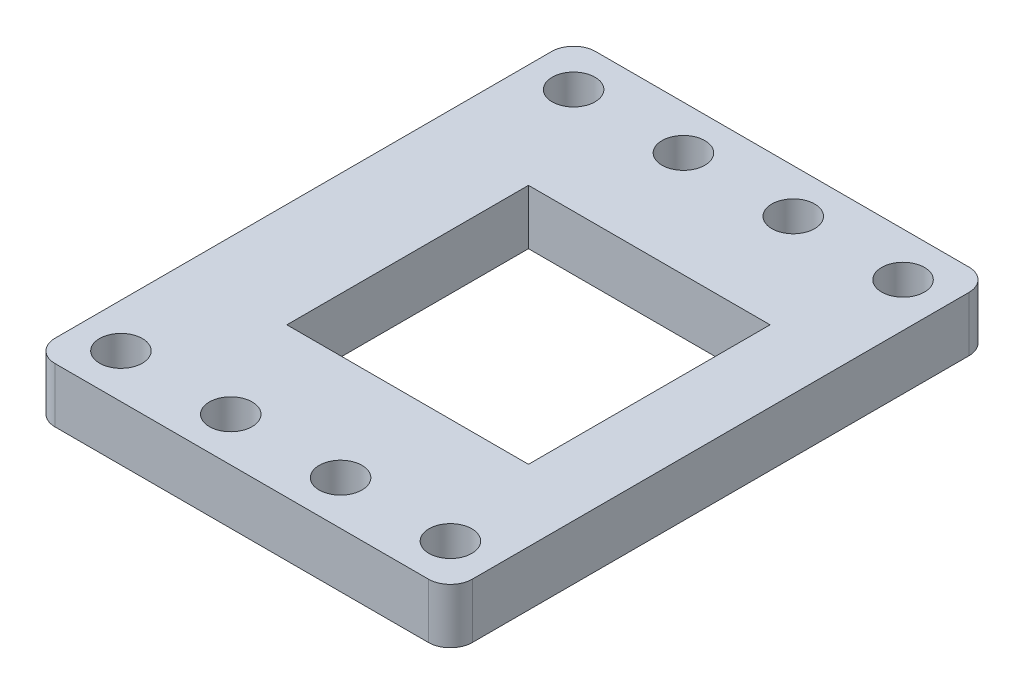
SolidWorks part; units mm, degrees
ref_plane "Front Plane" through (0, 0, 0) normal (0, 0, 1) x (1, 0, 0)
ref_plane "Top Plane" through (0, 0, 0) normal (0, 1, 0) x (1, 0, 0)
ref_plane "Right Plane" through (0, 0, 0) normal (1, 0, 0) x (0, 0, -1)
sketch "Sketch1" plane through (0, 0, 0) normal (0, 1, 0) x (1, 0, 0)
  line L1 (-36, 0) -> (-2, 0)
  line L2 (-38, -2) -> (-38, -47.22)
  line L3 (-36, -49.22) -> (-2, -49.22)
  line L4 (0, -2) -> (0, -47.22)
  arc A0 (-2, -49.22) -> (0, -47.22) centre (-2, -47.22) ccw
  arc A1 (-38, -47.22) -> (-36, -49.22) centre (-36, -47.22) ccw
  arc A2 (-36, 0) -> (-38, -2) centre (-36, -2) ccw
  arc A3 (-2, 0) -> (0, -2) centre (-2, -2) cw
  point P7 (0, -49.22)
  point P12 (-38, 0)
  point P15 (0, 0)
  dimension "D3" = 2
  dimension "D1" = 38
  dimension "D2" = 49.22
extrude "Boss-Extrude1" add sketch "Sketch1" along normal blind 5
sketch "Sketch2" plane through (0, 5, 0) normal (0, 1, 0) x (1, 0, 0)
  line L0 (-2, 0) -> (-36, 0) construction
  line L1 (0, -47.22) -> (0, -2) construction
  line L2 (-4, -4) -> (-54, -4) construction
  line L4 (-4, -45.22) -> (-54, -45.22) construction
  line L5 (-36, -49.22) -> (-2, -49.22) construction
  line L6 (-28.5, -24.61) -> (-6.5, -24.61) construction
  line L7 (-28.5, -13.61) -> (-6.5, -13.61)
  line L8 (-28.5, -13.61) -> (-28.5, -35.61)
  line L9 (-28.5, -35.61) -> (-6.5, -35.61)
  line L10 (-6.5, -13.61) -> (-6.5, -35.61)
  circle A20 centre (-4, -4) radius 1.95
  circle A21 centre (-14, -4) radius 1.95
  circle A22 centre (-24, -4) radius 1.95
  circle A23 centre (-54, -4) radius 1.95
  circle A24 centre (-34, -4) radius 1.95
  circle A25 centre (-44, -4) radius 1.95
  circle A26 centre (-44, -45.22) radius 1.95
  circle A27 centre (-34, -45.22) radius 1.95
  circle A28 centre (-54, -45.22) radius 1.95
  circle A29 centre (-24, -45.22) radius 1.95
  circle A30 centre (-14, -45.22) radius 1.95
  circle A31 centre (-4, -45.22) radius 1.95
  dimension "D1" = 10
  dimension "D7" = 3.9
  dimension "D8" = 3.9
  dimension "D9" = 3.9
  dimension "D10" = 10
  dimension "D11" = 10
  dimension "D12" = 10
  dimension "D13" = 4
  dimension "D14" = 4
  dimension "D3" = 3.9
  dimension "D5" = 3.9
  dimension "D6" = 3.9
  dimension "D2" = 10
  dimension "D42" = 22
  dimension "D43" = 6.5
  dimension "D44" = 22
extrude "Cut-Extrude1" cut sketch "Sketch2" against normal through all
